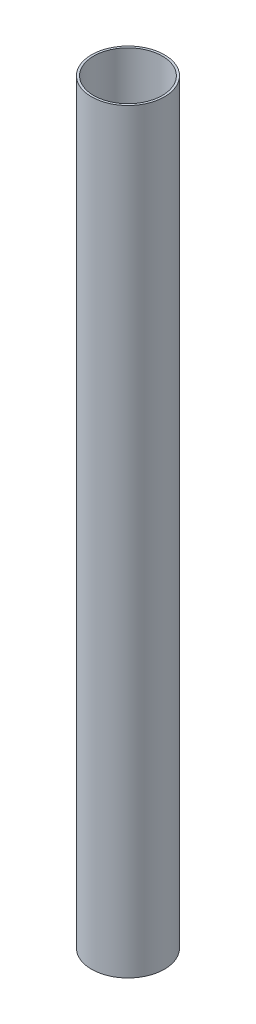
SolidWorks part; units mm, degrees
ref_plane "Front Plane" through (0, 0, 0) normal (0, 0, 1) x (1, 0, 0)
ref_plane "Top Plane" through (0, 0, 0) normal (0, 1, 0) x (1, 0, 0)
ref_plane "Right Plane" through (0, 0, 0) normal (1, 0, 0) x (0, 0, -1)
sketch "Sketch1" plane through (0, 0, 0) normal (0, 0, 1) x (1, 0, 0)
  line L1 (49.53, 1092.2) -> (52.705, 1092.2)
  line L2 (49.53, 1092.2) -> (49.53, 0)
  line L3 (49.53, 0) -> (52.705, 0)
  line L4 (52.705, 1092.2) -> (52.705, 0)
  dimension "D1" = 0
  dimension "D2" = 49.53
  dimension "D3" = 3.175
  dimension "D4" = 1092.2
ref_axis "Central Axis" through (0, 1146.81, 0) along (0, -1, 0)
revolve "Revolve1" add sketch "Sketch1" angle 360 about axis through (0, 1146.81, 0) along (0, -1, 0)
ref_plane "fin plane 1" through (0, 0, 0) normal (-0.866, 0, 0.5) x (0, -1, 0)
ref_plane "fin plane 2" through (0, 0, 0) normal (0.866, 0, 0.5) x (0, -1, 0)
